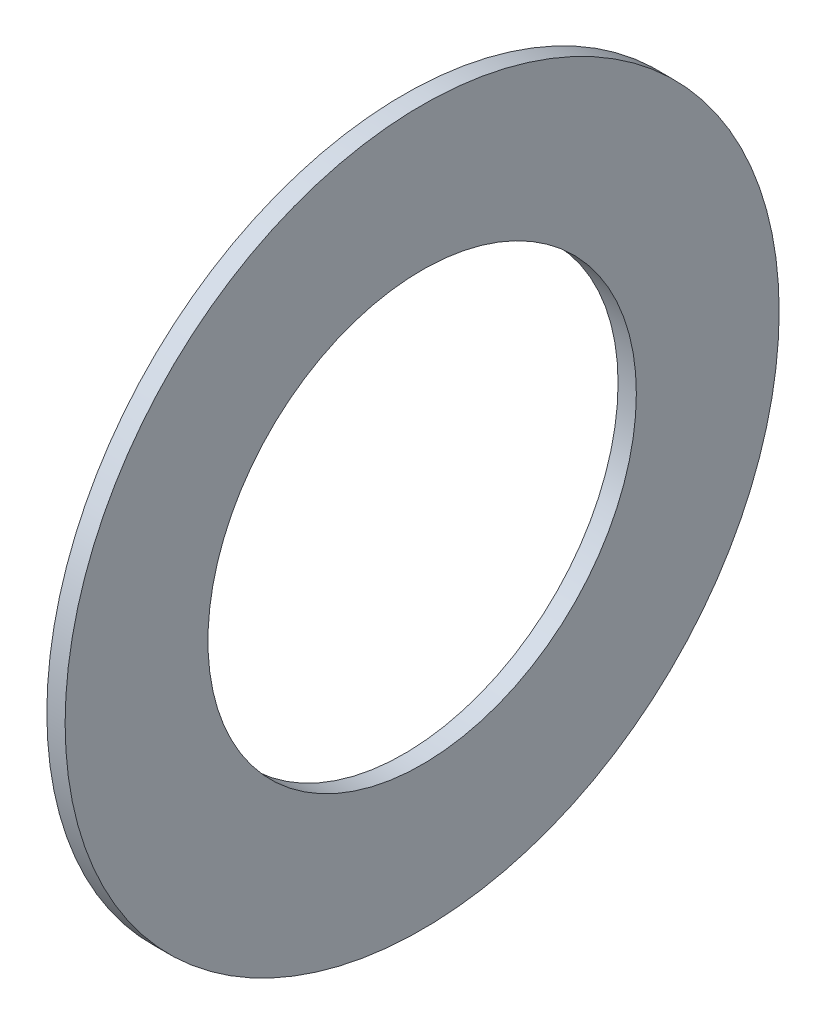
SolidWorks part; units mm, degrees
material "Plain Carbon Steel"
ref_plane "Front Plane" through (0, 0, 0) normal (0, 0, 1) x (1, 0, 0)
ref_plane "Top Plane" through (0, 0, 0) normal (0, 1, 0) x (1, 0, 0)
ref_plane "Right Plane" through (0, 0, 0) normal (1, 0, 0) x (0, 0, -1)
sketch "Sketch1" plane through (0, 0, 0) normal (1, 0, 0) x (0, 0, -1)
  circle A0 centre (0, 0) radius 15.875
  circle A1 centre (0, 0) radius 9.525
  dimension "OD" = 31.75
  dimension "Shaft Dia" = 19.05
extrude "Extrude1" add sketch "Sketch1" along normal blind 0.8128
